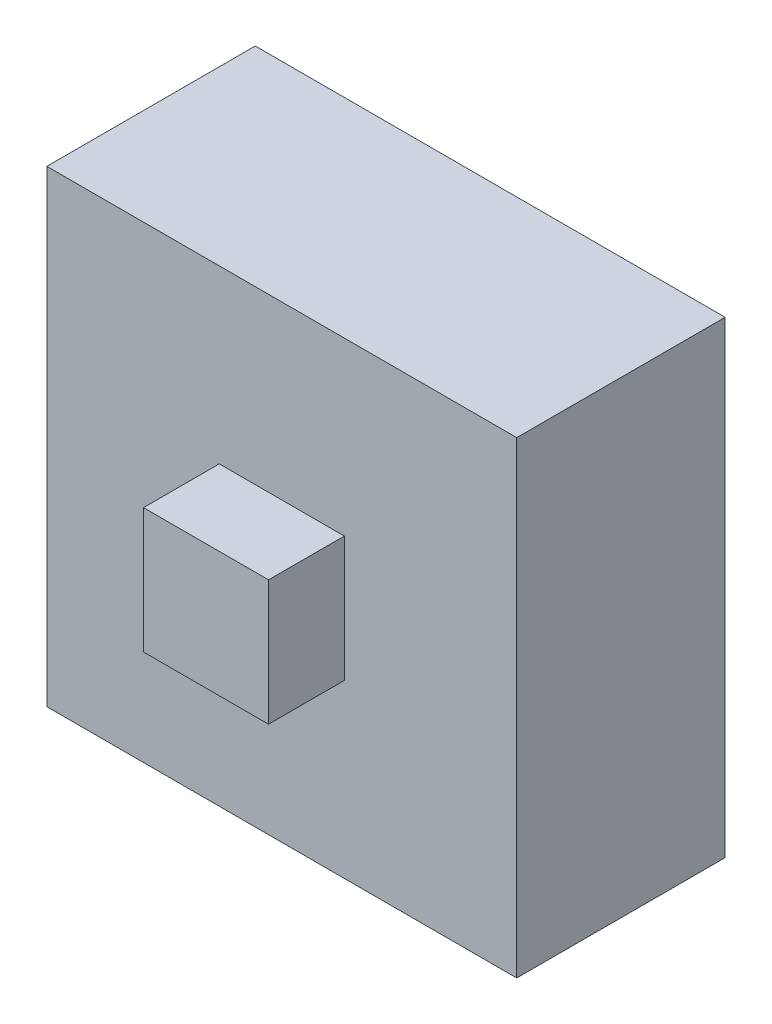
SolidWorks part; units mm, degrees
ref_plane "Front Plane" through (0, 0, 0) normal (0, 0, 1) x (1, 0, 0)
ref_plane "Top Plane" through (0, 0, 0) normal (0, 1, 0) x (1, 0, 0)
ref_plane "Right Plane" through (0, 0, 0) normal (1, 0, 0) x (0, 0, -1)
sketch "Sketch1" plane through (0, 0, 0) normal (0, 0, 1) x (1, 0, 0)
  line L0 (6.1415, 8.1234) -> (2.8415, 8.1234)
  line L1 (2.8415, 8.1234) -> (2.8415, 5.6234)
  line L2 (2.8415, 5.6234) -> (3.6415, 4.8234)
  line L3 (3.6415, 4.8234) -> (5.3415, 4.8234)
  line L4 (5.3415, 4.8234) -> (6.1415, 5.6234)
  line L5 (6.1415, 5.6234) -> (6.1415, 8.1234)
extrude "Boss-Extrude1" add sketch "Sketch1" along normal blind 3
sketch "Sketch3" plane through (0, 0, -22.1152) normal (0, 0, 1) x (1, 0, 0)
  line L0 (-0.7085, 11.6484) -> (-0.7085, 1.2984)
  line L1 (-0.7085, 1.2984) -> (9.6915, 1.2984)
  line L2 (9.6915, 1.2984) -> (9.6915, 11.6484)
  line L3 (9.6915, 11.6484) -> (-0.7085, 11.6484)
  line L4 (2.8415, 8.1234) -> (2.8415, 5.6234)
  line L5 (2.8415, 8.1234) -> (2.8415, 5.6234) construction
  line L6 (6.1415, 8.1234) -> (2.8415, 8.1234) construction
  line L7 (2.8415, 5.6234) -> (3.6415, 4.8234)
  line L8 (2.8415, 5.6234) -> (3.6415, 4.8234) construction
  line L9 (3.6415, 4.8234) -> (5.3415, 4.8234)
  line L10 (5.3415, 4.8234) -> (6.1415, 5.6234) construction
  line L11 (5.3415, 4.8234) -> (6.1415, 5.6234)
  line L12 (6.1415, 5.6234) -> (6.1415, 8.1234) construction
  line L13 (6.1415, 5.6234) -> (6.1415, 8.1234)
  line L14 (6.1415, 8.1234) -> (2.8415, 8.1234)
extrude "Boss-Extrude2" add sketch "Sketch3" against normal blind 3 and the other way blind 1 from vertex at 22.1152 starting at point (2.8415, 8.1234, 0)
sketch "Sketch4" plane through (0, 0, 1) normal (0, 0, 1) x (1, 0, 0)
  line L0 (-0.7085, 11.6484) -> (-0.7085, 1.2984) construction
  line L4 (-0.7085, 1.2984) -> (9.6915, 1.2984) construction
  line L5 (-0.7085, 4.5984) -> (-0.7085, 1.2984)
  line L6 (-0.7085, 1.2984) -> (2.5915, 1.2984)
  line L12 (9.6915, 1.2984) -> (6.3915, 1.2984)
  line L13 (9.6915, 4.5984) -> (9.6915, 1.2984)
  line L14 (9.6915, 8.3484) -> (9.6915, 11.6484)
  line L15 (9.6915, 11.6484) -> (6.3915, 11.6484)
  line L16 (-0.7085, 8.3484) -> (-0.7085, 11.6484)
  line L17 (-0.7085, 11.6484) -> (2.5915, 11.6484)
  arc A0 (-0.7085, 4.5984) -> (2.5915, 1.2984) centre (-0.7085, 1.2984) cw
  arc A1 (9.6915, 4.5984) -> (6.3915, 1.2984) centre (9.6915, 1.2984) ccw
  arc A2 (9.6915, 8.3484) -> (6.3915, 11.6484) centre (9.6915, 11.6484) cw
  arc A3 (-0.7085, 8.3484) -> (2.5915, 11.6484) centre (-0.7085, 11.6484) ccw
extrude "Cut-Extrude1" cut sketch "Sketch4" against normal up to surface (4 mm away) up to face at (4.4915, 6.19, -3)
sketch "Sketch5" plane through (0, 0, 3) normal (0, 0, 1) x (1, 0, 0)
  line L0 (2.8415, 5.6234) -> (3.6415, 4.8234)
  line L1 (2.8415, 5.6234) -> (3.6415, 4.8234) construction
  line L2 (2.8415, 8.1234) -> (2.8415, 5.6234) construction
  line L3 (3.6415, 4.8234) -> (2.8415, 4.8234)
  line L4 (2.8415, 4.8234) -> (2.8415, 5.6234)
  line L5 (5.3415, 4.8234) -> (6.1415, 5.6234)
  line L6 (3.6415, 4.8234) -> (5.3415, 4.8234) construction
  line L7 (5.3415, 4.8234) -> (6.1415, 5.6234) construction
  line L8 (6.1415, 5.6234) -> (6.1415, 4.8234)
  line L9 (6.1415, 4.8234) -> (5.3415, 4.8234)
extrude "Boss-Extrude3" add sketch "Sketch5" against normal up to surface (2 mm away) up to face at (4.4915, 6.4734, 1)
ref_plane "Plane1" through (2.5915, 1.2984, 1) normal (0, 0, 1) x (1, 0, 0)
sketch "Sketch6" plane through (-0.7085, 0, 0) normal (-1, 0, 0) x (0, 0, 1)
  line L4 (1, 4.5984) -> (1, 8.3484)
  line L5 (1, 8.3484) -> (-3, 8.3484)
  line L6 (-3, 8.3484) -> (-3, 4.5984)
  line L7 (-3, 4.5984) -> (1, 4.5984)
  line L8 (1, 4.5984) -> (1, 8.3484)
  line L9 (1, 8.3484) -> (-3, 8.3484)
  line L10 (-3, 8.3484) -> (-3, 4.5984)
  line L11 (-3, 4.5984) -> (1, 4.5984)
  dimension "D1" = 0
extrude "Boss-Extrude4" add sketch "Sketch6" along normal blind 1
sketch "Sketch7" plane through (9.6915, 0, 0) normal (1, 0, 0) x (0, 0, -1)
  line L4 (3, 4.5984) -> (3, 8.3484)
  line L5 (3, 8.3484) -> (-1, 8.3484)
  line L6 (-1, 8.3484) -> (-1, 4.5984)
  line L7 (-1, 4.5984) -> (3, 4.5984)
  line L8 (3, 4.5984) -> (3, 8.3484)
  line L9 (3, 8.3484) -> (-1, 8.3484)
  line L10 (-1, 8.3484) -> (-1, 4.5984)
  line L11 (-1, 4.5984) -> (3, 4.5984)
  dimension "D1" = 0
extrude "Boss-Extrude5" add sketch "Sketch7" along normal blind 1
sketch "Sketch8" plane through (0, 11.6484, 0) normal (0, 1, 0) x (1, 0, 0)
  line L4 (6.3915, 3) -> (2.5915, 3)
  line L5 (2.5915, 3) -> (2.5915, -1)
  line L6 (2.5915, -1) -> (6.3915, -1)
  line L7 (6.3915, -1) -> (6.3915, 3)
  line L8 (6.3915, 3) -> (2.5915, 3)
  line L9 (2.5915, 3) -> (2.5915, -1)
  line L10 (2.5915, -1) -> (6.3915, -1)
  line L11 (6.3915, -1) -> (6.3915, 3)
  dimension "D1" = 0
extrude "Boss-Extrude6" add sketch "Sketch8" along normal blind 1
sketch "Sketch9" plane through (0, 1.2984, 0) normal (0, -1, 0) x (1, 0, 0)
  line L4 (2.5915, -3) -> (6.3915, -3)
  line L5 (6.3915, -3) -> (6.3915, 1)
  line L6 (6.3915, 1) -> (2.5915, 1)
  line L7 (2.5915, 1) -> (2.5915, -3)
  line L8 (2.5915, -3) -> (6.3915, -3)
  line L9 (6.3915, -3) -> (6.3915, 1)
  line L10 (6.3915, 1) -> (2.5915, 1)
  line L11 (2.5915, 1) -> (2.5915, -3)
  dimension "D1" = 0
extrude "Boss-Extrude7" add sketch "Sketch9" along normal blind 1
sketch "Sketch10" plane through (0, 0, -3) normal (0, 0, -1) x (-1, 0, 0)
  line L8 (-6.6415, 6.8734) -> (-6.6415, 8.6234)
  line L9 (-6.6415, 8.6234) -> (-4.4915, 8.6234)
  line L10 (-2.3415, 8.6234) -> (-2.3415, 6.8734)
  line L11 (-4.4915, 8.6234) -> (-2.3415, 8.6234)
  line L12 (-6.6415, 6.8734) -> (-6.6415, 5.6234)
  line L13 (-6.6415, 5.6234) -> (-5.8415, 4.8234)
  line L14 (-5.8415, 4.8234) -> (-5.3415, 4.3234)
  line L15 (-5.3415, 4.3234) -> (-4.4915, 4.3234)
  line L16 (-2.3415, 6.8734) -> (-2.3415, 5.6234)
  line L17 (-2.3415, 5.6234) -> (-3.6415, 4.3234)
  line L18 (-3.6415, 4.3234) -> (-4.4915, 4.3234)
extrude "Cut-Extrude2" cut sketch "Sketch10" against normal up to vertex (3 mm away)
sketch "Sketch11" plane through (0, 0, -3) normal (0, 0, -1) x (-1, 0, 0)
  line L0 (-6.6415, 5.6234) -> (-5.3415, 4.3234) construction
  line L1 (-5.3415, 4.3234) -> (-3.6415, 4.3234) construction
  line L2 (-3.6415, 4.3234) -> (-2.3415, 5.6234) construction
  line L3 (-2.3415, 5.6234) -> (-2.3415, 8.6234) construction
  line L4 (-2.3415, 8.6234) -> (-6.6415, 8.6234) construction
  line L5 (-6.6415, 8.6234) -> (-6.6415, 5.6234) construction
  line L6 (-6.6415, 5.6234) -> (-5.3415, 4.3234)
  line L7 (-5.3415, 4.3234) -> (-3.6415, 4.3234)
  line L8 (-3.6415, 4.3234) -> (-2.3415, 5.6234)
  line L9 (-2.3415, 5.6234) -> (-2.3415, 8.6234)
  line L10 (-2.3415, 8.6234) -> (-6.6415, 8.6234)
  line L11 (-6.6415, 8.6234) -> (-6.6415, 5.6234)
  line L12 (0.7085, 4.5984) -> (1.7085, 4.5984)
  line L13 (1.7085, 4.5984) -> (1.7085, 8.3484)
  line L14 (1.7085, 8.3484) -> (0.7085, 8.3484)
  line L15 (-2.5915, 11.6484) -> (-2.5915, 12.6484)
  line L16 (-2.5915, 12.6484) -> (-6.3915, 12.6484)
  line L17 (-6.3915, 12.6484) -> (-6.3915, 11.6484)
  line L18 (-9.6915, 8.3484) -> (-10.6915, 8.3484)
  line L19 (-10.6915, 8.3484) -> (-10.6915, 4.5984)
  line L20 (-10.6915, 4.5984) -> (-9.6915, 4.5984)
  line L21 (-6.3915, 1.2984) -> (-6.3915, 0.2984)
  line L22 (-6.3915, 0.2984) -> (-2.5915, 0.2984)
  line L23 (-2.5915, 0.2984) -> (-2.5915, 1.2984)
  line L24 (0.7085, 4.5984) -> (1.7085, 4.5984)
  line L25 (1.7085, 4.5984) -> (1.7085, 8.3484)
  line L26 (1.7085, 8.3484) -> (0.7085, 8.3484)
  line L27 (-2.5915, 11.6484) -> (-2.5915, 12.6484)
  line L28 (-2.5915, 12.6484) -> (-6.3915, 12.6484)
  line L29 (-6.3915, 12.6484) -> (-6.3915, 11.6484)
  line L30 (-9.6915, 8.3484) -> (-10.6915, 8.3484)
  line L31 (-10.6915, 8.3484) -> (-10.6915, 4.5984)
  line L32 (-10.6915, 4.5984) -> (-9.6915, 4.5984)
  line L33 (-6.3915, 1.2984) -> (-6.3915, 0.2984)
  line L34 (-6.3915, 0.2984) -> (-2.5915, 0.2984)
  line L35 (-2.5915, 0.2984) -> (-2.5915, 1.2984)
  arc A4 (0.7085, 4.5984) -> (-2.5915, 1.2984) centre (0.7085, 1.2984) ccw
  arc A5 (-2.5915, 11.6484) -> (0.7085, 8.3484) centre (0.7085, 11.6484) ccw
  arc A6 (-9.6915, 8.3484) -> (-6.3915, 11.6484) centre (-9.6915, 11.6484) ccw
  arc A7 (-6.3915, 1.2984) -> (-9.6915, 4.5984) centre (-9.6915, 1.2984) ccw
  arc A8 (0.7085, 4.5984) -> (-2.5915, 1.2984) centre (0.7085, 1.2984) ccw
  arc A9 (-2.5915, 11.6484) -> (0.7085, 8.3484) centre (0.7085, 11.6484) ccw
  arc A10 (-9.6915, 8.3484) -> (-6.3915, 11.6484) centre (-9.6915, 11.6484) ccw
  arc A11 (-6.3915, 1.2984) -> (-9.6915, 4.5984) centre (-9.6915, 1.2984) ccw
  dimension "D1" = 0
extrude "Boss-Extrude8" add sketch "Sketch11" along normal blind 3
sketch "Sketch13" plane through (0, 0, -6) normal (0, 0, -1) x (-1, 0, 0)
  line L0 (-2.3415, 8.6234) -> (-6.6415, 8.6234) construction
  line L2 (-2.3415, 8.6234) -> (-6.6415, 8.6234)
  line L4 (-2.3415, 5.6234) -> (-2.3415, 8.6234) construction
  line L6 (-3.6415, 4.3234) -> (-2.3415, 5.6234) construction
  line L8 (-5.3415, 4.3234) -> (-3.6415, 4.3234) construction
  line L10 (-6.6415, 5.6234) -> (-5.3415, 4.3234) construction
  line L12 (-6.3915, 7.1234) -> (-6.3915, 8.3734)
  line L13 (-6.3915, 8.3734) -> (-4.4915, 8.3734)
  line L14 (-2.5915, 8.3734) -> (-2.5915, 7.1234)
  line L15 (-3.1683, 5.1501) -> (-2.5915, 5.7269)
  line L16 (-2.5915, 5.7269) -> (-2.5915, 7.1234)
  line L17 (-4.4915, 8.3734) -> (-2.5915, 8.3734)
  line L18 (-6.3915, 7.1234) -> (-6.3915, 5.7269)
  line L19 (-6.3915, 5.7269) -> (-5.8147, 5.1501)
  line L20 (-5.8147, 5.1501) -> (-5.238, 4.5734)
  line L21 (-5.238, 4.5734) -> (-4.4915, 4.5734)
  line L22 (-3.1683, 5.1501) -> (-3.7451, 4.5734)
  line L23 (-3.7451, 4.5734) -> (-4.4915, 4.5734)
  line L24 (-6.6415, 8.6234) -> (-6.6415, 5.6234) construction
  line L25 (-2.3415, 5.6234) -> (-2.3415, 8.6234)
  line L26 (-3.6415, 4.3234) -> (-2.3415, 5.6234)
  line L27 (-5.3415, 4.3234) -> (-3.6415, 4.3234)
  line L28 (-6.6415, 5.6234) -> (-5.3415, 4.3234)
  line L29 (-6.6415, 8.6234) -> (-6.6415, 5.6234)
extrude "Boss-Extrude9" add sketch "Sketch13" against normal up to vertex (6 mm away)
sketch "Sketch14" plane through (0, 0, -6) normal (0, 0, -1) x (-1, 0, 0)
  line L0 (-6.3915, 5.7269) -> (-5.238, 4.5734) construction
  line L1 (-5.238, 4.5734) -> (-3.7451, 4.5734) construction
  line L2 (-3.7451, 4.5734) -> (-2.5915, 5.7269) construction
  line L3 (-2.5915, 5.7269) -> (-2.5915, 8.3734) construction
  line L4 (-2.5915, 8.3734) -> (-6.3915, 8.3734) construction
  line L5 (-6.3915, 8.3734) -> (-6.3915, 5.7269) construction
  line L6 (-6.3915, 5.7269) -> (-5.238, 4.5734)
  line L7 (-5.238, 4.5734) -> (-3.7451, 4.5734)
  line L8 (-3.7451, 4.5734) -> (-2.5915, 5.7269)
  line L9 (-2.5915, 5.7269) -> (-2.5915, 8.3734)
  line L10 (-2.5915, 8.3734) -> (-6.3915, 8.3734)
  line L11 (-6.3915, 8.3734) -> (-6.3915, 5.7269)
  line L12 (0.7085, 4.5984) -> (1.7085, 4.5984)
  line L13 (1.7085, 4.5984) -> (1.7085, 8.3484)
  line L14 (1.7085, 8.3484) -> (0.7085, 8.3484)
  line L15 (-2.5915, 11.6484) -> (-2.5915, 12.6484)
  line L16 (-2.5915, 12.6484) -> (-6.3915, 12.6484)
  line L17 (-6.3915, 12.6484) -> (-6.3915, 11.6484)
  line L18 (-9.6915, 8.3484) -> (-10.6915, 8.3484)
  line L19 (-10.6915, 8.3484) -> (-10.6915, 4.5984)
  line L20 (-10.6915, 4.5984) -> (-9.6915, 4.5984)
  line L21 (-6.3915, 1.2984) -> (-6.3915, 0.2984)
  line L22 (-6.3915, 0.2984) -> (-2.5915, 0.2984)
  line L23 (-2.5915, 0.2984) -> (-2.5915, 1.2984)
  line L25 (1.7085, 4.5984) -> (1.7085, 8.3484)
  line L28 (-2.5915, 12.6484) -> (-6.3915, 12.6484)
  line L31 (-10.6915, 8.3484) -> (-10.6915, 4.5984)
  line L34 (-6.3915, 0.2984) -> (-2.5915, 0.2984)
  line L36 (-10.6915, 8.3484) -> (-10.6915, 12.6484)
  line L37 (-10.6915, 12.6484) -> (-6.3915, 12.6484)
  line L38 (-2.5915, 12.6484) -> (1.7085, 12.6484)
  line L39 (1.7085, 12.6484) -> (1.7085, 8.3484)
  line L40 (1.7085, 4.5984) -> (1.7085, 0.2984)
  line L41 (1.7085, 0.2984) -> (-2.5915, 0.2984)
  line L42 (-6.3915, 0.2984) -> (-10.6915, 0.2984)
  line L43 (-10.6915, 0.2984) -> (-10.6915, 4.5984)
  arc A4 (0.7085, 4.5984) -> (-2.5915, 1.2984) centre (0.7085, 1.2984) ccw
  arc A5 (-2.5915, 11.6484) -> (0.7085, 8.3484) centre (0.7085, 11.6484) ccw
  arc A6 (-9.6915, 8.3484) -> (-6.3915, 11.6484) centre (-9.6915, 11.6484) ccw
  arc A7 (-6.3915, 1.2984) -> (-9.6915, 4.5984) centre (-9.6915, 1.2984) ccw
  dimension "D1" = 0
extrude "Boss-Extrude10" add sketch "Sketch14" against normal up to surface (7 mm away)
sketch "Sketch15" plane through (0, 0, -6) normal (0, 0, -1) x (-1, 0, 0)
  line L4 (-10.6915, 0.2984) -> (1.7085, 0.2984)
  line L5 (1.7085, 0.2984) -> (1.7085, 12.6484)
  line L6 (1.7085, 12.6484) -> (-10.6915, 12.6484)
  line L7 (-10.6915, 12.6484) -> (-10.6915, 0.2984)
  line L8 (-10.6915, 0.2984) -> (1.7085, 0.2984)
  line L9 (1.7085, 0.2984) -> (1.7085, 12.6484)
  line L10 (1.7085, 12.6484) -> (-10.6915, 12.6484)
  line L11 (-10.6915, 12.6484) -> (-10.6915, 0.2984)
  dimension "D1" = 0
extrude "Cut-Extrude3" cut sketch "Sketch15" against normal blind 1.5
